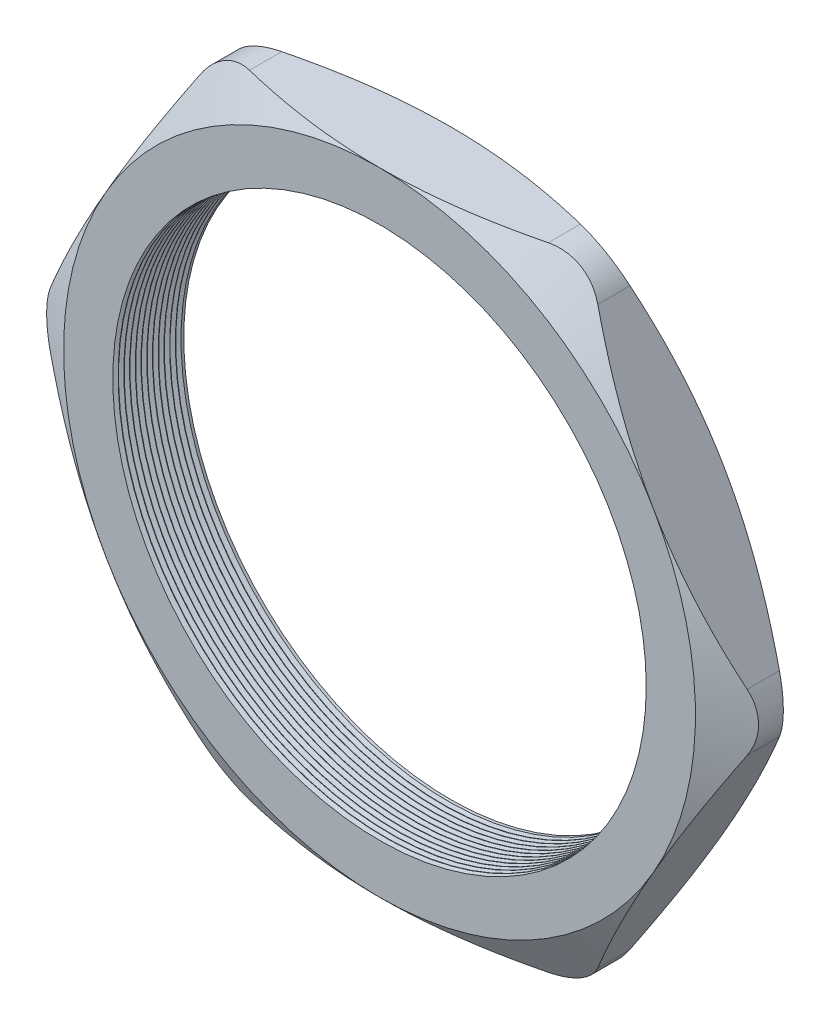
SolidWorks part; units mm, degrees
ref_plane "Front Plane" through (0, 0, 0) normal (0, 0, 1) x (1, 0, 0)
ref_plane "Top Plane" through (0, 0, 0) normal (0, 1, 0) x (1, 0, 0)
ref_plane "Right Plane" through (0, 0, 0) normal (1, 0, 0) x (0, 0, -1)
sketch "Sketch1" plane through (0, 0, 0) normal (0, 0, 1) x (1, 0, 0)
  line L1 (-40.4746, 0) -> (-20.2373, -35.052)
  line L2 (-20.2373, -35.052) -> (20.2373, -35.052)
  line L3 (20.2373, -35.052) -> (40.4746, 0)
  line L4 (40.4746, 0) -> (20.2373, 35.052)
  line L5 (20.2373, 35.052) -> (-20.2373, 35.052)
  line L6 (-20.2373, 35.052) -> (-40.4746, 0)
  circle A0 centre (0, 0) radius 35.052 construction
  circle A1 centre (0, 0) radius 29.591
  dimension "TS" = 59.182
  dimension "H" = 70.104
extrude "Extrude1" add sketch "Sketch1" along normal blind 7.874
sketch "Sketch2" plane through (0, 0, 7.874) normal (0, 0, 1) x (1, 0, 0)
  line L0 (20.2373, 35.052) -> (-20.2373, 35.052) construction
  circle A0 centre (0, 0) radius 35.052
extrude "Cut-Extrude1" cut sketch "Sketch2" against normal through all draft 60 flip side to cut
sketch "Sketch3" plane through (0, 0, 0) normal (0, 0, -1) x (-1, 0, 0)
  line L0 (-20.2373, 35.052) -> (20.2373, 35.052) construction
  circle A0 centre (0, 0) radius 35.052
extrude "Cut-Extrude2" cut sketch "Sketch3" against normal through all draft 60 flip side to cut
fillet "Fillet1" radius 6.35 6 edges at (40.4746, 0, 3.937) (20.2373, -35.052, 3.937) (-20.2373, -35.052, 3.937) (-40.4746, 0, 3.937) (-20.2373, 35.052, 3.937) (20.2373, 35.052, 3.937)
sketch "Sketch4" plane through (0, 0, 0) normal (0, 1, 0) x (1, 0, 0)
  line L0 (-29.591, -7.874) -> (-29.591, -7.2874)
  line L1 (-29.591, 0) -> (-29.591, -7.874) construction
  line L2 (-29.591, -7.2874) -> (-30.099, -7.5807)
  line L3 (-30.099, -7.5807) -> (-29.591, -7.874)
  dimension "D1" = 60
  dimension "D2" = 60
  dimension "D3" = 0.508
revolve "Cut-Revolve1" cut sketch "Sketch4" angle 360 about axis through (0, 0, 0) along (0, 0, 1)
pattern_linear "LPattern1" count 12 spacing 0.635 along (0, 0, -1) of "Cut-Revolve1"
